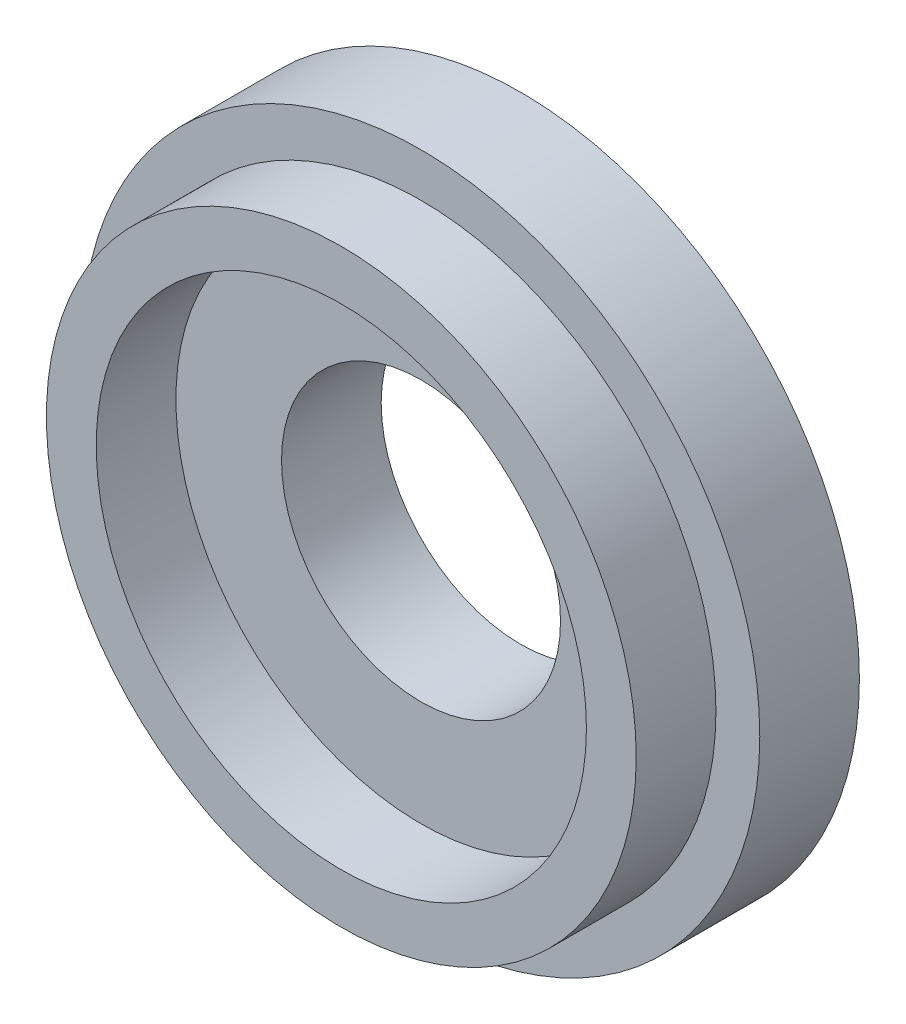
SolidWorks part; units mm, degrees
ref_plane "Front Plane" through (0, 0, 0) normal (0, 0, 1) x (1, 0, 0)
ref_plane "Top Plane" through (0, 0, 0) normal (0, 1, 0) x (1, 0, 0)
ref_plane "Right Plane" through (0, 0, 0) normal (1, 0, 0) x (0, 0, -1)
sketch "Sketch1" plane through (0, 0, 0) normal (1, 0, 0) x (0, 0, -1)
  line L0 (-52.9749, 0) -> (54.0739, 0) construction
  line L1 (-4.4095, 7.4) -> (-4.4095, 8.5)
  line L2 (-4.4095, 3.5) -> (-1.9095, 3.5)
  line L3 (-4.4095, 4.25) -> (-4.4095, 6.15)
  line L4 (-4.4095, 8.5) -> (-1.9095, 8.5)
  line L5 (-1.9095, 3.5) -> (-1.9095, 8.5)
  line L6 (-4.4095, 3.5) -> (-1.9095, 8.5) construction
  line L7 (-4.4095, 8.5) -> (-1.9095, 3.5) construction
  line L9 (-4.4095, 3.5) -> (-4.4095, 4.25)
  line L10 (-6.4095, 7.4) -> (-4.4095, 7.4)
  line L11 (-6.4095, 7.4) -> (-6.4095, 6.15)
  line L12 (-6.4095, 6.15) -> (-4.4095, 6.15)
  point P3 (-3.1595, 6)
  point P8 (0.5495, 0)
  dimension "D1" = 3.5
  dimension "D2" = 5
  dimension "D3" = 2.5
  dimension "D4" = 2.65
  dimension "D5" = 1.25
  dimension "D6" = 2
revolve "Revolve1" add sketch "Sketch1" angle 360 about L0
